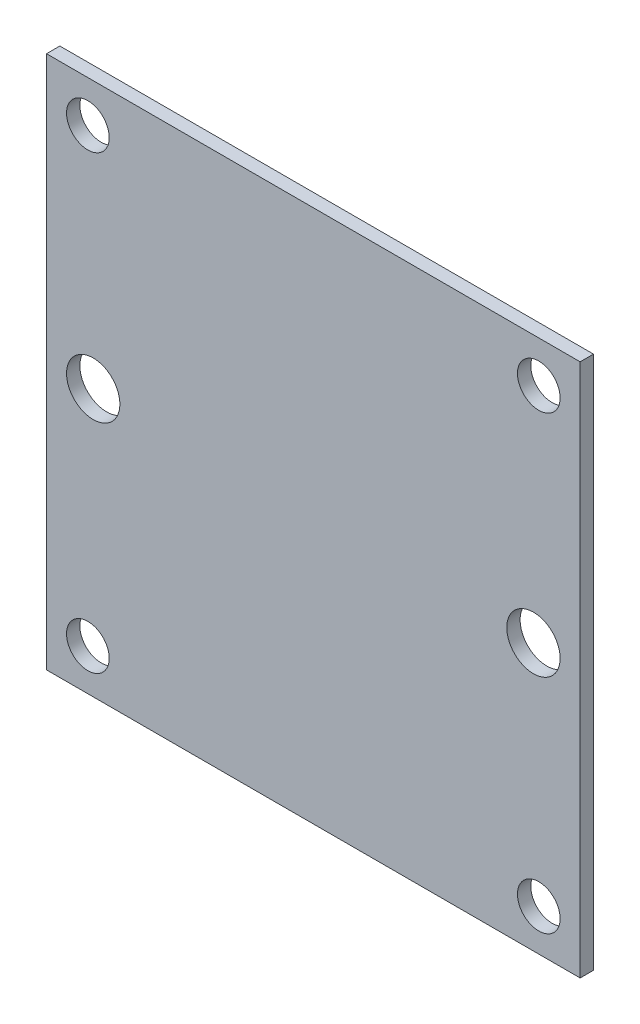
SolidWorks part; units mm, degrees
ref_plane "Front Plane" through (0, 0, 0) normal (0, 0, 1) x (1, 0, 0)
ref_plane "Top Plane" through (0, 0, 0) normal (0, 1, 0) x (1, 0, 0)
ref_plane "Right Plane" through (0, 0, 0) normal (1, 0, 0) x (0, 0, -1)
sketch "Sketch1" plane through (0, 0, 0) normal (0, 0, 1) x (1, 0, 0)
  line L1 (-20, 20) -> (20, 20)
  line L2 (-20, 20) -> (-20, -20)
  line L3 (-20, -20) -> (20, -20)
  line L4 (20, 20) -> (20, -20)
  line L5 (-20, 20) -> (20, -20) construction
  line L6 (-20, -20) -> (20, 20) construction
  point P0 (0, 0)
  dimension "D1" = 40
  dimension "D2" = 40
extrude "Boss-Extrude1" add sketch "Sketch1" along normal blind 1
sketch "Sketch2" plane through (0, 0, 1) normal (0, 0, 1) x (1, 0, 0)
  line L0 (-20, 20) -> (-20, -20) construction
  line L1 (20, 20) -> (-20, 20) construction
  line L2 (20, -20) -> (20, 20) construction
  line L3 (-20, -20) -> (20, -20) construction
  circle A0 centre (-16.9, -16.9) radius 1.6
  circle A1 centre (16.9, -16.9) radius 1.6
  circle A2 centre (16.9, 16.9) radius 1.6
  circle A3 centre (-16.9, 16.9) radius 1.6
  circle A5 centre (16.5, 0) radius 2
  circle A7 centre (-16.5, 0) radius 2
  dimension "D1" = 3.5
  dimension "D5" = 3.1
  dimension "D6" = 20
  dimension "D2" = 3.1
  dimension "D3" = 3.5
  dimension "D4" = 3.1
  dimension "D7" = 3.1
extrude "Cut-Extrude1" cut sketch "Sketch2" against normal blind 10
